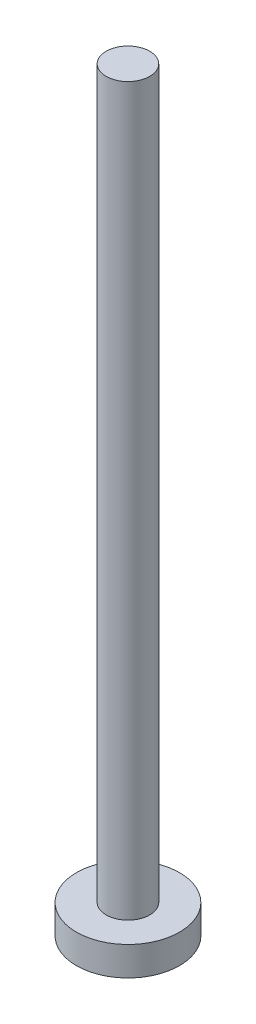
SolidWorks part; units mm, degrees
ref_plane "前视基准面" through (0, 0, 0) normal (0, 0, 1) x (1, 0, 0)
ref_plane "上视基准面" through (0, 0, 0) normal (0, 1, 0) x (1, 0, 0)
ref_plane "右视基准面" through (0, 0, 0) normal (1, 0, 0) x (0, 0, -1)
sketch "草图1" plane through (0, 0, 0) normal (0, 1, 0) x (1, 0, 0)
  circle A0 centre (0, 0) radius 3.55
  dimension "D1" = 7.1
extrude "凸台-拉伸1" add sketch "草图1" along normal blind 2
sketch "草图2" plane through (0, 2, 0) normal (0, 1, 0) x (1, 0, 0)
  circle A0 centre (0, 0) radius 1.5
  dimension "D1" = 3
extrude "凸台-拉伸2" add sketch "草图2" along normal blind 50
